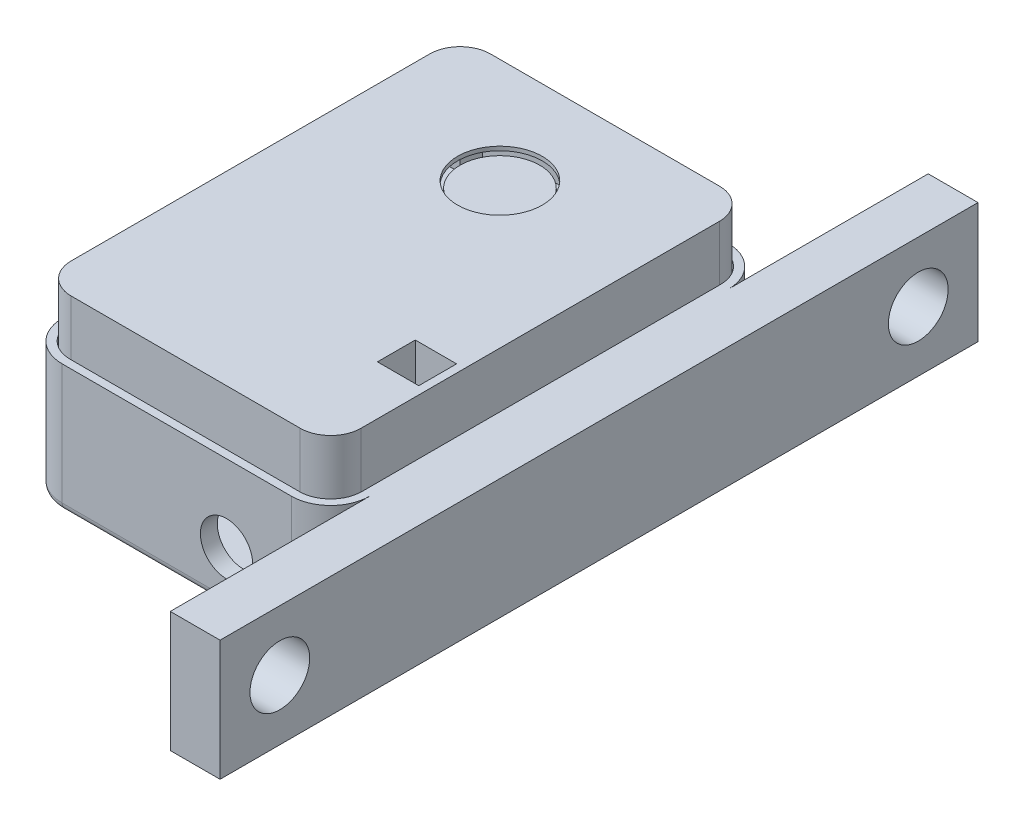
SolidWorks part; units mm, degrees
other "Front Lid"
other "ESP32 Cam"
other "Rear Lid"
ref_plane "Front Plane" through (0, 0, 0) normal (0, 0, 1) x (1, 0, 0)
ref_plane "Top Plane" through (0, 0, 0) normal (0, 1, 0) x (1, 0, 0)
ref_plane "Right Plane" through (0, 0, 0) normal (1, 0, 0) x (0, 0, -1)
sketch "Sketch1" plane through (0, 0, 0) normal (0, 1, 0) x (1, 0, 0)
  line L1 (-11.5, 20) -> (11.5, 20)
  line L2 (-13.5, 18) -> (-13.5, -18)
  line L3 (-11.5, -20) -> (11.5, -20)
  line L4 (13.5, 18) -> (13.5, -18)
  line L5 (-13.5, 20) -> (13.5, -20) construction
  line L6 (-13.5, -20) -> (13.5, 20) construction
  arc A0 (-11.5, 20) -> (-13.5, 18) centre (-11.5, 18) ccw
  arc A1 (11.5, 20) -> (13.5, 18) centre (11.5, 18) cw
  arc A2 (11.5, -20) -> (13.5, -18) centre (11.5, -18) ccw
  arc A3 (-13.5, -18) -> (-11.5, -20) centre (-11.5, -18) ccw
  point P0 (0, 0)
  dimension "D3" = 2
  dimension "D1" = 27
  dimension "D2" = 40
extrude "Boss-Extrude1" add sketch "Sketch1" along normal blind 1
sketch "Sketch2" plane through (0, 1, 0) normal (0, 1, 0) x (1, 0, 0)
  line L0 (0, 0) -> (0, 20) construction
  line L1 (11.5, 20) -> (-11.5, 20) construction
  line L3 (-7.5, 20) -> (7.5, 20)
  line L4 (-7.5, 20) -> (-7.5, 5)
  line L5 (-7.5, 5) -> (7.5, 5)
  line L6 (7.5, 20) -> (7.5, 5)
  line L7 (-7.5, 20) -> (7.5, 5) construction
  line L8 (-7.5, 5) -> (7.5, 20) construction
  point P5 (0, 12.5)
  dimension "D1" = 15
extrude "Boss-Extrude2" add sketch "Sketch2" along normal blind 2
sketch "Sketch3" plane through (0, 3, 0) normal (0, 1, 0) x (1, 0, 0)
  line L0 (0, 5) -> (0, 20) construction
  line L1 (-7.5, 5) -> (7.5, 5) construction
  line L2 (7.5, 20) -> (-7.5, 20) construction
  circle A0 centre (0, 10.5) radius 4
  dimension "D1" = 8
  dimension "D2" = 5.5
extrude "Boss-Extrude3" add sketch "Sketch3" along normal blind 6.25
sketch "Sketch5" plane through (0, 1, 0) normal (0, 1, 0) x (1, 0, 0)
  line L0 (-11.5, -20) -> (11.5, -20) construction
  line L1 (10, -8) -> (13, -8)
  line L2 (10, -8) -> (10, -11)
  line L3 (10, -11) -> (13, -11)
  line L4 (13, -8) -> (13, -11)
  line L5 (10, -8) -> (13, -11) construction
  line L6 (10, -11) -> (13, -8) construction
  line L7 (13.5, -18) -> (13.5, 18) construction
  point P0 (11.5, -9.5)
  dimension "D1" = 3
  dimension "D2" = 10.5
  dimension "D3" = 2
extrude "Boss-Extrude4" add sketch "Sketch5" along normal blind 1
sketch "Sketch6" plane through (0, 9.25, 0) normal (0, 1, 0) x (1, 0, 0)
  line L37 (7.5, 21.05) -> (-7.5, 21.05)
  line L38 (-7.5, 21.05) -> (-11.5, 21.05)
  line L39 (-14.55, 18) -> (-14.55, -18)
  line L40 (-11.5, -21.05) -> (11.5, -21.05)
  line L41 (14.55, -18) -> (14.55, 18)
  line L42 (11.5, 21.05) -> (7.5, 21.05)
  line L43 (7.5, 20.25) -> (-7.5, 20.25)
  line L44 (11.5, 20.25) -> (7.5, 20.25)
  line L45 (13.75, -18) -> (13.75, 18)
  line L46 (-11.5, -20.25) -> (11.5, -20.25)
  line L47 (-13.75, 18) -> (-13.75, -18)
  line L48 (-7.5, 20.25) -> (-11.5, 20.25)
  line L55 (7.5, 20.25) -> (-7.5, 20.25) construction
  line L56 (11.5, 20.25) -> (7.5, 20.25) construction
  line L57 (13.75, -18) -> (13.75, 18) construction
  line L58 (-11.5, -20.25) -> (11.5, -20.25) construction
  line L59 (-13.75, 18) -> (-13.75, -18) construction
  line L60 (-7.5, 20.25) -> (-11.5, 20.25) construction
  circle A6 centre (0, 10.5) radius 4.25
  circle A8 centre (0, 10.5) radius 4.25
  arc A36 (-11.5, 21.05) -> (-14.55, 18) centre (-11.5, 18) ccw
  arc A37 (-14.55, -18) -> (-11.5, -21.05) centre (-11.5, -18) ccw
  arc A38 (11.5, -21.05) -> (14.55, -18) centre (11.5, -18) ccw
  arc A39 (14.55, 18) -> (11.5, 21.05) centre (11.5, 18) ccw
  arc A40 (13.75, 18) -> (11.5, 20.25) centre (11.5, 18) ccw
  arc A41 (11.5, -20.25) -> (13.75, -18) centre (11.5, -18) ccw
  arc A42 (-13.75, -18) -> (-11.5, -20.25) centre (-11.5, -18) ccw
  arc A43 (-11.5, 20.25) -> (-13.75, 18) centre (-11.5, 18) ccw
  arc A44 (13.75, 18) -> (11.5, 20.25) centre (11.5, 18) ccw construction
  arc A45 (11.5, -20.25) -> (13.75, -18) centre (11.5, -18) ccw construction
  arc A46 (-13.75, -18) -> (-11.5, -20.25) centre (-11.5, -18) ccw construction
  arc A47 (-11.5, 20.25) -> (-13.75, 18) centre (-11.5, 18) ccw construction
  dimension "D1" = 0.25
  dimension "D2" = 0.8
  dimension "D3" = 0.25
extrude "Boss-Extrude5" add sketch "Sketch6" along normal blind 0.4 from offset 0.25 separate body
sketch "Sketch8" plane through (0, 9.5, 0) normal (0, -1, 0) x (1, 0, 0)
  line L4 (-11.5, -21.05) -> (11.5, -21.05)
  line L5 (14.55, -18) -> (14.55, 18)
  line L6 (11.5, 21.05) -> (-11.5, 21.05)
  line L7 (-14.55, 18) -> (-14.55, -18)
  line L8 (-11.5, -21.05) -> (11.5, -21.05)
  line L9 (14.55, -18) -> (14.55, 18)
  line L10 (11.5, 21.05) -> (-11.5, 21.05)
  line L11 (-14.55, 18) -> (-14.55, -18)
  line L16 (-11.5, -20.25) -> (11.5, -20.25)
  line L17 (13.75, -18) -> (13.75, 18)
  line L18 (11.5, 20.25) -> (-11.5, 20.25)
  line L19 (-13.75, 18) -> (-13.75, -18)
  line L20 (-11.5, -20.25) -> (11.5, -20.25)
  line L21 (13.75, -18) -> (13.75, 18)
  line L22 (11.5, 20.25) -> (-11.5, 20.25)
  line L23 (-13.75, 18) -> (-13.75, -18)
  arc A4 (11.5, -21.05) -> (14.55, -18) centre (11.5, -18) ccw
  arc A5 (14.55, 18) -> (11.5, 21.05) centre (11.5, 18) ccw
  arc A6 (-11.5, 21.05) -> (-14.55, 18) centre (-11.5, 18) ccw
  arc A7 (-14.55, -18) -> (-11.5, -21.05) centre (-11.5, -18) ccw
  arc A8 (11.5, -21.05) -> (14.55, -18) centre (11.5, -18) ccw
  arc A9 (14.55, 18) -> (11.5, 21.05) centre (11.5, 18) ccw
  arc A10 (-11.5, 21.05) -> (-14.55, 18) centre (-11.5, 18) ccw
  arc A11 (-14.55, -18) -> (-11.5, -21.05) centre (-11.5, -18) ccw
  arc A16 (11.5, -20.25) -> (13.75, -18) centre (11.5, -18) ccw
  arc A17 (13.75, 18) -> (11.5, 20.25) centre (11.5, 18) ccw
  arc A18 (-11.5, 20.25) -> (-13.75, 18) centre (-11.5, 18) ccw
  arc A19 (-13.75, -18) -> (-11.5, -20.25) centre (-11.5, -18) ccw
  arc A20 (11.5, -20.25) -> (13.75, -18) centre (11.5, -18) ccw
  arc A21 (13.75, 18) -> (11.5, 20.25) centre (11.5, 18) ccw
  arc A22 (-11.5, 20.25) -> (-13.75, 18) centre (-11.5, 18) ccw
  arc A23 (-13.75, -18) -> (-11.5, -20.25) centre (-11.5, -18) ccw
  dimension "D1" = 0
  dimension "D2" = 0.8
extrude "Boss-Extrude7" add sketch "Sketch8" along normal up to vertex (9.5 mm away) up to point (-11.5, 0, 20)
sketch "Sketch9" plane through (0, 9.5, 0) normal (0, -1, 0) x (1, 0, 0)
  line L0 (13.75, 18) -> (11.5, 18)
  line L1 (11.5, 18) -> (11.5, 20.25)
  line L2 (5.445, 0) -> (-5.445, 0) construction
  line L3 (11.5, -18) -> (11.5, -20.25)
  line L4 (13.75, -18) -> (11.5, -18)
  line L5 (0, -5.445) -> (0, 5.445) construction
  line L6 (-13.75, -18) -> (-11.5, -18)
  line L7 (-11.5, -18) -> (-11.5, -20.25)
  line L8 (-11.5, 18) -> (-11.5, 20.25)
  line L9 (-13.75, 18) -> (-11.5, 18)
  arc A0 (13.75, 18) -> (11.5, 20.25) centre (11.5, 18) ccw construction
  arc A1 (13.75, 18) -> (11.5, 20.25) centre (11.5, 18) ccw
  arc A2 (13.75, -18) -> (11.5, -20.25) centre (11.5, -18) cw
  arc A3 (-13.75, -18) -> (-11.5, -20.25) centre (-11.5, -18) ccw
  arc A4 (-13.75, 18) -> (-11.5, 20.25) centre (-11.5, 18) cw
extrude "Boss-Extrude9" add sketch "Sketch9" along normal offset from surface (8.4 mm away) 0.1 up to face at (0, 1, -4.1667)
sketch "Sketch11" plane through (0, 9.9, 0) normal (0, 1, 0) x (1, 0, 0)
  line L1 (13.75, -7.6) -> (9.6, -7.6)
  line L2 (9.6, -7.6) -> (9.6, -11.4)
  line L3 (9.6, -11.4) -> (13.75, -11.4)
  line L4 (13, -11) -> (13, -8)
  line L5 (13, -8) -> (10, -8)
  line L6 (10, -8) -> (10, -11)
  line L7 (10, -11) -> (13, -11)
  line L8 (13, -11) -> (13, -8) construction
  line L9 (13, -8) -> (10, -8) construction
  line L10 (10, -8) -> (10, -11) construction
  line L11 (10, -11) -> (13, -11) construction
  line L12 (13.75, 18) -> (13.75, -18) construction
  line L13 (13.75, -7.6) -> (13.75, -11.4)
  line L14 (9.6, -11.4) -> (13.4, -11.4) construction
  line L15 (13.4, -11.4) -> (13.4, -7.6) construction
  line L16 (13.4, -7.6) -> (9.6, -7.6) construction
  dimension "D1" = 0
  dimension "D2" = 0.4
extrude "Cut-Extrude1" cut sketch "Sketch11" against normal up to vertex (0.4 mm away) up to point (11.5, 9.5, 18)
sketch "Sketch12" plane through (0, 0, 0) normal (0, -1, 0) x (1, 0, 0)
  line L0 (0, 0) -> (0, 20) construction
  line L1 (-11.5, 20) -> (11.5, 20) construction
  line L3 (9.375, -5.65) -> (-9.375, -5.65)
  line L4 (9.375, -5.65) -> (9.375, 20)
  line L5 (9.375, 20) -> (-9.375, 20)
  line L6 (-9.375, -5.65) -> (-9.375, 20)
  line L7 (9.375, -5.65) -> (-9.375, 20) construction
  line L8 (9.375, 20) -> (-9.375, -5.65) construction
  point P5 (0, 7.175)
  dimension "D1" = 18.75
  dimension "D2" = 25.65
extrude "Boss-Extrude10" add sketch "Sketch12" along normal blind 0.75
sketch "Sketch13" plane through (0, -0.75, 0) normal (0, -1, 0) x (1, 0, 0)
  line L0 (0, -5.65) -> (0, 20) construction
  line L1 (-9.375, -5.65) -> (9.375, -5.65) construction
  line L2 (8, 12.35) -> (2, 12.35) construction
  line L3 (2, 12.35) -> (-8, 12.35)
  line L4 (8, 9.35) -> (8, -5.15)
  line L5 (8, -5.15) -> (-8, -5.15)
  line L6 (-8, 12.35) -> (-8, -5.15)
  line L7 (8, 12.35) -> (-8, -5.15) construction
  line L8 (8, -5.15) -> (-8, 12.35) construction
  line L11 (8, 9.35) -> (2, 9.35)
  line L12 (2, 12.35) -> (2, 9.35)
  line L13 (8, 12.35) -> (8, 9.35) construction
  line L14 (9.375, 20) -> (11.5, 20) construction
  point P5 (0, 3.6)
  dimension "D1" = 16
  dimension "D2" = 17.5
  dimension "D3" = 3
  dimension "D4" = 6
  dimension "D5" = 0.5
extrude "Boss-Extrude11" add sketch "Sketch13" along normal blind 2.3
sketch "Sketch14" plane through (0, 0, 0) normal (0, -1, 0) x (1, 0, 0)
  line L0 (9.375, 20) -> (11.5, 20) construction
  line L1 (12.75, -16.2) -> (10.25, -16.2)
  line L2 (12.75, -16.2) -> (12.75, 4)
  line L3 (12.75, 4) -> (10.25, 4)
  line L4 (10.25, -16.2) -> (10.25, 4)
  line L5 (12.75, -16.2) -> (10.25, 4) construction
  line L6 (12.75, 4) -> (10.25, -16.2) construction
  line L7 (13.5, 18) -> (13.5, -18) construction
  point P0 (11.5, -6.1)
  dimension "D1" = 20.2
  dimension "D2" = 2.5
  dimension "D3" = 16
  dimension "D4" = 0.75
extrude "Boss-Extrude12" add sketch "Sketch14" along normal blind 2.45
sketch "Sketch16" plane through (0, -2.45, 0) normal (0, -1, 0) x (1, 0, 0)
  line L0 (11.5, 4) -> (11.5, -16.2) construction
  line L3 (11.2, 3) -> (11.8, 3)
  line L8 (11.2, 3) -> (11.2, 2.4)
  line L9 (11.2, 2.4) -> (11.8, 2.4)
  line L10 (11.8, 3) -> (11.8, 2.4)
  line L11 (12.75, 4) -> (10.25, 4) construction
  line L12 (10.25, -16.2) -> (12.75, -16.2) construction
  dimension "D1" = 0.6
  dimension "D2" = 1
extrude "Boss-Extrude14" add sketch "Sketch16" along normal blind 5.5
pattern_linear "LPattern1" count 8 spacing 2.5 along (0, 0, -1) of "Boss-Extrude14"
sketch "Sketch17" plane through (0, -3.05, 0) normal (0, -1, 0) x (1, 0, 0)
  line L14 (-11.5, -21.95) -> (11.5, -21.95)
  line L15 (15.45, -18) -> (15.45, 18)
  line L16 (-11.5, -21.15) -> (11.5, -21.15)
  line L17 (-14.65, 18) -> (-14.65, -18)
  line L18 (11.5, 21.15) -> (-11.5, 21.15)
  line L19 (-11.5, -21.15) -> (11.5, -21.15)
  line L20 (-14.65, 18) -> (-14.65, -18)
  line L21 (11.5, 21.15) -> (-11.5, 21.15)
  line L22 (14.65, -18) -> (14.65, 18)
  line L23 (11.5, 21.95) -> (-11.5, 21.95)
  line L24 (-15.45, 18) -> (-15.45, -18)
  arc A16 (11.5, -21.95) -> (15.45, -18) centre (11.5, -18) ccw
  arc A17 (15.45, 18) -> (11.5, 21.95) centre (11.5, 18) ccw
  arc A18 (-11.5, 21.95) -> (-15.45, 18) centre (-11.5, 18) ccw
  arc A19 (-15.45, -18) -> (-11.5, -21.95) centre (-11.5, -18) ccw
  arc A20 (11.5, -21.15) -> (14.65, -18) centre (11.5, -18) ccw
  arc A21 (-14.65, -18) -> (-11.5, -21.15) centre (-11.5, -18) ccw
  arc A22 (-11.5, 21.15) -> (-14.65, 18) centre (-11.5, 18) ccw
  arc A23 (14.65, 18) -> (11.5, 21.15) centre (11.5, 18) ccw
  arc A24 (11.5, -21.15) -> (14.65, -18) centre (11.5, -18) ccw
  arc A25 (-14.65, -18) -> (-11.5, -21.15) centre (-11.5, -18) ccw
  arc A26 (-11.5, 21.15) -> (-14.65, 18) centre (-11.5, 18) ccw
  arc A27 (14.65, 18) -> (11.5, 21.15) centre (11.5, 18) ccw
  dimension "D1" = 0.1
  dimension "D2" = 0.8
extrude "Boss-Extrude15" add sketch "Sketch17" against normal blind 12.5 from offset 5 separate body
sketch "Sketch18" plane through (0, -8.05, 0) normal (0, -1, 0) x (1, 0, 0)
  line L0 (-11.5, -20.25) -> (11.5, -20.25) construction
  line L1 (-13.75, 18) -> (-13.75, -18) construction
  line L2 (13.75, -18) -> (13.75, 18) construction
  line L3 (11.5, 20.25) -> (-11.5, 20.25) construction
  line L4 (-11.5, -20.25) -> (11.5, -20.25)
  line L5 (-13.75, 18) -> (-13.75, -18)
  line L6 (13.75, -18) -> (13.75, 18)
  line L7 (11.5, 20.25) -> (-11.5, 20.25)
  line L8 (-11.5, -21.15) -> (11.5, -21.15) construction
  line L9 (-14.65, 18) -> (-14.65, -18) construction
  line L10 (11.5, 21.15) -> (-11.5, 21.15) construction
  line L11 (14.65, -18) -> (14.65, 18) construction
  line L12 (-11.5, -21.15) -> (11.5, -21.15)
  line L13 (-14.65, 18) -> (-14.65, -18)
  line L14 (11.5, 21.15) -> (-11.5, 21.15)
  line L15 (14.65, -18) -> (14.65, 18)
  arc A0 (11.5, -20.25) -> (13.75, -18) centre (11.5, -18) ccw construction
  arc A1 (-13.75, -18) -> (-11.5, -20.25) centre (-11.5, -18) ccw construction
  arc A2 (-11.5, 20.25) -> (-13.75, 18) centre (-11.5, 18) ccw construction
  arc A3 (13.75, 18) -> (11.5, 20.25) centre (11.5, 18) ccw construction
  arc A4 (11.5, -20.25) -> (13.75, -18) centre (11.5, -18) ccw
  arc A5 (-13.75, -18) -> (-11.5, -20.25) centre (-11.5, -18) ccw
  arc A6 (-11.5, 20.25) -> (-13.75, 18) centre (-11.5, 18) ccw
  arc A7 (13.75, 18) -> (11.5, 20.25) centre (11.5, 18) ccw
  arc A8 (11.5, -21.15) -> (14.65, -18) centre (11.5, -18) ccw construction
  arc A9 (-14.65, -18) -> (-11.5, -21.15) centre (-11.5, -18) ccw construction
  arc A10 (-11.5, 21.15) -> (-14.65, 18) centre (-11.5, 18) ccw construction
  arc A11 (14.65, 18) -> (11.5, 21.15) centre (11.5, 18) ccw construction
  arc A12 (11.5, -21.15) -> (14.65, -18) centre (11.5, -18) ccw
  arc A13 (-14.65, -18) -> (-11.5, -21.15) centre (-11.5, -18) ccw
  arc A14 (-11.5, 21.15) -> (-14.65, 18) centre (-11.5, 18) ccw
  arc A15 (14.65, 18) -> (11.5, 21.15) centre (11.5, 18) ccw
extrude "Boss-Extrude16" add sketch "Sketch18" against normal offset from surface (7.95 mm away) 0.1 up to face at (0, 0, 0)
sketch "Sketch19" plane through (0, -8.05, 0) normal (0, -1, 0) x (1, 0, 0)
  line L165 (0, -5.445) -> (0, 5.445) construction
  line L166 (-13.25, -16.7) -> (-13.25, 4.5)
  line L167 (-13.25, 4.5) -> (-9.75, 4.5)
  line L168 (-9.75, 4.5) -> (-9.75, -16.7)
  line L169 (13.25, 4.5) -> (9.75, 4.5)
  line L170 (13.25, -16.7) -> (13.25, 4.5)
  line L171 (9.75, -16.7) -> (13.25, -16.7)
  line L172 (9.75, 4.5) -> (9.75, -16.7)
  line L173 (13.25, 4.5) -> (9.75, 4.5)
  line L174 (13.25, -16.7) -> (13.25, 4.5)
  line L175 (9.75, -16.7) -> (13.25, -16.7)
  line L176 (9.75, 4.5) -> (9.75, -16.7)
  line L177 (-9.75, -16.7) -> (-13.25, -16.7)
  line L178 (11.5, 21.95) -> (-11.5, 21.95) construction
  line L179 (-15.45, 18) -> (-15.45, -18) construction
  line L180 (-11.5, -21.95) -> (11.5, -21.95) construction
  line L181 (15.45, -18) -> (15.45, 18) construction
  line L182 (11.5, 21.95) -> (-11.5, 21.95)
  line L183 (-15.45, 18) -> (-15.45, -18)
  line L184 (-11.5, -21.95) -> (11.5, -21.95)
  line L185 (15.45, -18) -> (15.45, 18)
  arc A0 (15.45, 18) -> (11.5, 21.95) centre (11.5, 18) ccw construction
  arc A1 (-11.5, 21.95) -> (-15.45, 18) centre (-11.5, 18) ccw construction
  arc A2 (-15.45, -18) -> (-11.5, -21.95) centre (-11.5, -18) ccw construction
  arc A3 (11.5, -21.95) -> (15.45, -18) centre (11.5, -18) ccw construction
  arc A4 (15.45, 18) -> (11.5, 21.95) centre (11.5, 18) ccw
  arc A5 (-11.5, 21.95) -> (-15.45, 18) centre (-11.5, 18) ccw
  arc A6 (-15.45, -18) -> (-11.5, -21.95) centre (-11.5, -18) ccw
  arc A7 (11.5, -21.95) -> (15.45, -18) centre (11.5, -18) ccw
  dimension "D1" = 0.5
extrude "Boss-Extrude17" add sketch "Sketch19" along normal blind 0.4
sketch "Sketch20" plane through (0, 0, 21.95) normal (0, 0, 1) x (1, 0, 0)
  line L0 (2, -3.05) -> (2, -0.75) construction
  line L1 (8, -0.75) -> (2, -0.75) construction
  line L2 (8, -3.05) -> (8, -0.75) construction
  line L3 (8, -3.05) -> (2, -3.05) construction
  line L4 (2, -3.05) -> (2, -0.75) construction
  line L5 (8, -0.75) -> (2, -0.75) construction
  line L6 (8, -3.05) -> (8, -0.75) construction
  line L7 (8, -3.05) -> (2, -3.05) construction
  line L8 (8, -3.05) -> (2, -0.75) construction
  line L9 (8, -0.75) -> (2, -3.05) construction
  line L10 (5, -1.9) -> (5, -3.375) construction
  line L12 (9.375, -0.75) -> (-9.375, -0.75) construction
  line L13 (9.375, -0.75) -> (-9.375, -0.75) construction
  circle A0 centre (5, -3.375) radius 2.625
  dimension "D1" = 5.25
extrude "Cut-Extrude2" cut sketch "Sketch20" against normal up to next (1.7 mm away) contours A0
sketch "Sketch22" plane through (0, -8.05, 0) normal (0, 1, 0) x (1, 0, 0)
  line L0 (13.75, -18) -> (11.5, -18)
  line L1 (11.5, -18) -> (11.5, -20.25)
  line L2 (-5.445, 0) -> (5.445, 0) construction
  line L3 (11.5, 18) -> (11.5, 20.25)
  line L4 (13.75, 18) -> (11.5, 18)
  line L5 (0, -5.445) -> (0, 5.445) construction
  line L6 (-13.75, 18) -> (-11.5, 18)
  line L7 (-11.5, 18) -> (-11.5, 20.25)
  line L8 (-11.5, -18) -> (-11.5, -20.25)
  line L9 (-13.75, -18) -> (-11.5, -18)
  arc A0 (11.5, -20.25) -> (13.75, -18) centre (11.5, -18) ccw construction
  arc A1 (11.5, -20.25) -> (13.75, -18) centre (11.5, -18) ccw
  arc A2 (11.5, 20.25) -> (13.75, 18) centre (11.5, 18) cw
  arc A3 (-11.5, 20.25) -> (-13.75, 18) centre (-11.5, 18) ccw
  arc A4 (-11.5, -20.25) -> (-13.75, -18) centre (-11.5, -18) cw
extrude "Boss-Extrude18" add sketch "Sketch22" along normal up to vertex (6.05 mm away)
sketch "Sketch23" plane through (0, 9.5, 0) normal (0, -1, 0) x (1, 0, 0)
  line L1 (9.6, 11.4) -> (13.75, 11.4) construction
  line L2 (9.6, 7.6) -> (9.6, 11.4) construction
  line L3 (13.75, 7.6) -> (9.6, 7.6) construction
  line L5 (9.6, 11.4) -> (13.75, 11.4)
  line L6 (9.6, 7.6) -> (9.6, 11.4)
  line L7 (13.75, 7.6) -> (9.6, 7.6)
  line L8 (13.75, 6.8) -> (8.8, 6.8)
  line L9 (8.8, 6.8) -> (8.8, 12.2)
  line L10 (8.8, 12.2) -> (13.75, 12.2)
  line L11 (13.75, 7.6) -> (13.75, 6.8)
  line L12 (13.75, 12.2) -> (13.75, 11.4)
  dimension "D1" = 0.8
extrude "Boss-Extrude19" add sketch "Sketch23" along normal offset from surface (7.4 mm away) 1 up to face at (12.4053, 1.1, 18.9053)
mirror "Mirror1" about plane through (0, 0, 0) normal (1, 0, 0) of "LPattern1", "Boss-Extrude12", "Boss-Extrude14"
fillet "Fillet2" radius 0.8 8 edges at (-14.2931, -8.45, -20.7931) (-15.45, -8.45, 0) (-14.2931, -8.45, 20.7931) (0, -8.45, 21.95) (14.2931, -8.45, 20.7931) (15.45, -8.45, 0) (14.2931, -8.45, -20.7931) (0, -8.45, -21.95)
sketch "Sketch27" plane through (15.45, 0, 0) normal (1, 0, 0) x (0, 0, -1)
  line L0 (21.95, 4.45) -> (-38.05, 4.45)
  line L1 (-21.95, -7.65) -> (38.05, -7.65)
  line L3 (-38.05, 4.45) -> (38.05, 4.45)
  line L4 (-38.05, 4.45) -> (-38.05, -7.65)
  line L5 (-38.05, -7.65) -> (38.05, -7.65)
  line L6 (38.05, 4.45) -> (38.05, -7.65)
  line L7 (-18, -7.65) -> (18, -7.65) construction
  circle A0 centre (-32.05, -1.6) radius 3
  circle A1 centre (32.05, -1.6) radius 3
  line M5 (-18, 4.45) -> (-18, -7.65)
  line M6 (-18, -7.65) -> (18, -7.65)
  line M7 (18, -7.65) -> (18, 4.45)
  line M8 (18, 4.45) -> (-18, 4.45)
  dimension "D1" = 6.05
  dimension "D2" = 6.05
  dimension "D3" = 6
  dimension "D4" = 6
  dimension "D6" = 6
  dimension "D5" = 76.1
extrude "Boss-Extrude20" add sketch "Sketch27" along normal blind 5 contours L4 L5 L1 L0 A0 M5 | M8 M5 M6 M7 | L6 L3 L0 L1 A1 M7
